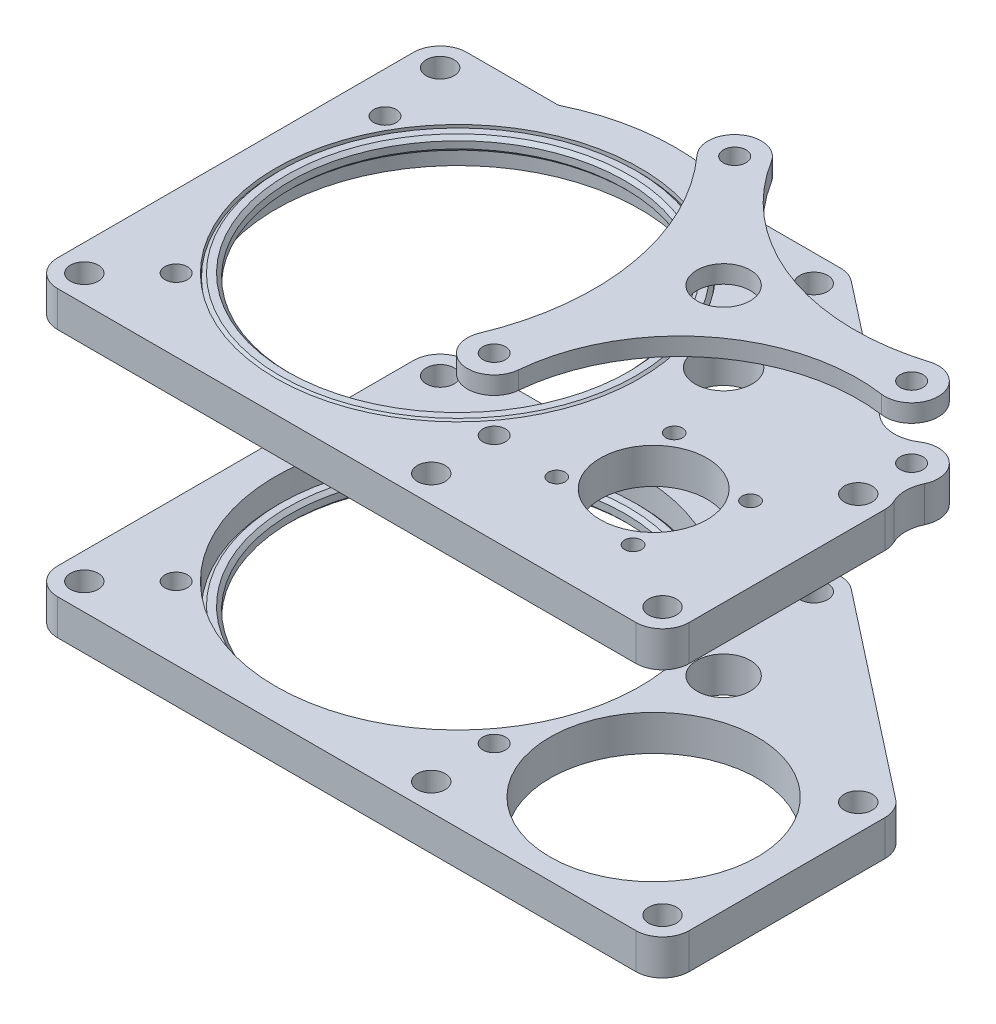
SolidWorks part; units mm, degrees
other "Stage 2 Retaining Plate"
other "Outer Top Plate"
other "Outer Bottom Plate"
other "Top Bearing Retainer"
other "Bottom Bearing Retainer"
material "Alum Plate"
ref_plane "Front Plane" through (0, 0, 0) normal (0, 0, 1) x (1, 0, 0)
ref_plane "Top Plane" through (0, 0, 0) normal (0, 1, 0) x (1, 0, 0)
ref_plane "Right Plane" through (0, 0, 0) normal (1, 0, 0) x (0, 0, -1)
other "Bounding Box"
ref_plane "Default Plane" through (-8.9266, -12.7485, 0) normal (-0.1736, 0.9848, 0) x (0.9848, 0.1736, 0)
sketch "Sketch1" plane through (0, 0, 0) normal (0, 1, 0) x (1, 0, 0)
  line L0 (-38.1, 76.2) -> (-38.1, -38.1)
  line L1 (-38.1, -38.1) -> (76.2, -38.1)
  line L2 (-38.1, 0) -> (0, 0) construction
  line L3 (0, 0) -> (0, -38.1) construction
  line L5 (-38.1, -38.1) -> (-33.3375, -33.3375) construction
  line L6 (-33.3375, -33.3375) -> (-33.3375, 0) construction
  line L7 (-33.3375, 0) -> (-33.3375, 30.1625) construction
  line L8 (-33.3375, -33.3375) -> (0, -33.3375) construction
  line L9 (0, -33.3375) -> (28.575, -33.3375) construction
  line L10 (28.575, -33.3375) -> (69.85, -33.3375) construction
  line L11 (-33.3375, 34.925) -> (-38.1, 34.925) construction
  circle A0 centre (0, 0) radius 32.5
  circle A1 centre (0, 0) radius 25
  circle A3 centre (50.8, -15.875) radius 17.5006
  circle A4 centre (0, 0) radius 31.115
  circle A5 centre (50.8, -15.875) radius 6.35
  circle A6 centre (38.3007, 9.1132) radius 8.255
  circle A7 centre (38.3007, 9.1132) radius 21.59
  circle A8 centre (-33.3375, -33.3375) radius 4.7625
  circle A9 centre (-33.3375, 30.1625) radius 4.7625
  circle A10 centre (69.85, -33.3375) radius 4.7625
  circle A12 centre (28.575, -33.3375) radius 4.7625
  point P24 (32.5, 0)
  point P26 (-32.5, 0)
  point P27 (33.2994, -15.875)
  point P38 (68.3006, -15.875)
  dimension "D1" = 65
  dimension "D2" = 50
  dimension "D3" = 35.0012
  dimension "D4" = 62.23
  dimension "D5" = 12.7
  dimension "D6" = 16.51
  dimension "D8" = 9.525
  dimension "D9" = 43.18
  dimension "D7" = 38.1
  dimension "D10" = 114.3
  dimension "D11" = 88.9
  dimension "D12" = 73.025
  dimension "D13" = 22.225
  dimension "D14" = 107.95
  dimension "D15" = 66.675
sketch "Sketch2" plane through (0, 0, 0) normal (0, 0, 1) x (1, 0, 0)
  line L0 (0, 0) -> (0, 19.05) construction
  line L1 (0, 19.05) -> (0, 24.1) construction
  line L2 (-32.5, 31.1) -> (32.5, 31.1)
  line L3 (-32.5, 31.1) -> (-32.5, 24.1)
  line L4 (-32.5, 24.1) -> (32.5, 24.1)
  line L5 (32.5, 31.1) -> (32.5, 24.1)
  line L6 (-32.5, 31.1) -> (32.5, 24.1) construction
  line L7 (-32.5, 24.1) -> (32.5, 31.1) construction
  line L8 (-32.5, 73.025) -> (32.5, 73.025)
  line L9 (-32.5, 73.025) -> (-32.5, 66.025)
  line L10 (-32.5, 66.025) -> (32.5, 66.025)
  line L11 (32.5, 73.025) -> (32.5, 66.025)
  line L12 (-32.5, 73.025) -> (32.5, 66.025) construction
  line L13 (-32.5, 66.025) -> (32.5, 73.025) construction
  line L14 (0, 31.1) -> (0, 66.025) construction
  line L15 (33.2994, 34.6047) -> (38.989, 24.75)
  line L16 (-38.1, 21.575) -> (101.6, 21.575)
  line L17 (-38.1, 21.575) -> (-38.1, 27.925)
  line L18 (-38.1, 27.925) -> (101.6, 27.925)
  line L19 (101.6, 21.575) -> (101.6, 27.925)
  line L20 (-38.1, 75.55) -> (101.6, 75.55)
  line L21 (-38.1, 75.55) -> (-38.1, 69.2)
  line L22 (-38.1, 69.2) -> (101.6, 69.2)
  line L23 (101.6, 75.55) -> (101.6, 69.2)
  line L24 (38.989, 24.75) -> (62.611, 24.75)
  line L25 (33.2994, 34.6047) -> (33.2994, 69.2)
  line L26 (33.2994, 69.2) -> (68.3006, 69.2)
  line L27 (68.3006, 34.6047) -> (68.3006, 69.2)
  line L28 (36.5821, 28.9189) -> (68.3006, 69.2) construction
  line L29 (33.2994, 69.2) -> (65.0179, 28.9189) construction
  line L30 (68.3006, 34.6047) -> (62.611, 24.75)
  line L31 (33.2994, 24.75) -> (33.2994, 34.6047) construction
  line L32 (33.2994, 24.75) -> (36.5821, 28.9189) construction
  line L33 (33.2994, 24.75) -> (38.989, 24.75) construction
  line L34 (62.611, 24.75) -> (68.3006, 24.75) construction
  line L35 (65.0179, 28.9189) -> (68.3006, 24.75) construction
  line L36 (68.3006, 24.75) -> (68.3006, 34.6047) construction
  line L37 (50.8, 24.75) -> (50.8, 69.2) construction
  line L38 (0, 0) -> (-69.131, 0) construction
  line L39 (-61.9887, 88.9) -> (127.3908, 88.9) construction
  line L40 (-32.5, 24.1) -> (-32.5, 21.575) construction
  line L41 (0, 88.25) -> (50.8, 88.25)
  line L42 (0, 88.25) -> (0, 85.075)
  line L43 (0, 85.075) -> (50.8, 85.075)
  line L44 (50.8, 88.25) -> (50.8, 85.075)
  line L45 (0, 88.25) -> (50.8, 85.075) construction
  line L46 (0, 85.075) -> (50.8, 88.25) construction
  line L47 (-32.5, 73.025) -> (-32.5, 75.55) construction
  circle A0 centre (0, 19.05) radius 19.05
  point P3 (0, 27.6)
  point P9 (0, 69.525)
  point P32 (50.8, 46.975)
  point P43 (25.4, 86.6625)
  dimension "D1" = 38.1
  dimension "D2" = 7
  dimension "D3" = 34.925
  dimension "D4" = 73.025
  dimension "D5" = 88.9
  dimension "D6" = 6.35
  dimension "D7" = 30
  dimension "D8" = 44.45
  dimension "D9" = 23.622
  dimension "D10" = 9.525
  dimension "D11" = 3.175
  dimension "D12" = 41.275
  dimension "D13" = 101.6
ref_plane "Plane1" through (0, 27.925, 0) normal (0, 1, 0) x (1, 0, 0)
sketch "Sketch3" plane through (0, 27.925, 0) normal (0, 1, 0) x (1, 0, 0)
  line L0 (-38.1, 76.2) -> (-38.1, -38.1) construction
  line L1 (-38.1, -38.1) -> (76.2, -38.1) construction
  line L2 (-38.1, 30.1625) -> (-38.1, -33.3375)
  line L3 (-33.3375, -38.1) -> (69.85, -38.1)
  line L5 (-33.3375, 30.1625) -> (33.3375, 30.1625) construction
  line L6 (69.85, -33.3375) -> (69.85, 1.5875) construction
  line L7 (0, 0) -> (0, 30.1625) construction
  line L8 (50.8, -15.875) -> (69.85, -15.875) construction
  line L9 (-33.3375, 34.925) -> (-17.0167, 34.925)
  line L10 (36.2727, 33.913) -> (72.7852, 5.338)
  line L11 (74.6125, 1.5875) -> (74.6125, -33.3375)
  line L12 (17.0167, 34.925) -> (33.3375, 34.925)
  circle A0 centre (0, 0) radius 32.5 construction
  circle A1 centre (0, 0) radius 32.5
  circle A3 centre (-33.3375, -33.3375) radius 4.7625 construction
  arc A5 (-38.1, -33.3375) -> (-33.3375, -38.1) centre (-33.3375, -33.3375) ccw
  circle A6 centre (-33.3375, 30.1625) radius 2.4892
  circle A8 centre (-33.3375, -33.3375) radius 2.4892
  circle A9 centre (28.575, -33.3375) radius 2.4892
  circle A10 centre (50.8, -15.875) radius 18.5166
  circle A11 centre (38.3007, 9.1132) radius 4.7625
  circle A12 centre (50.8, -15.875) radius 17.5006 construction
  circle A13 centre (69.85, -33.3375) radius 2.4892
  circle A14 centre (69.85, 1.5875) radius 2.4892
  circle A15 centre (33.3375, 30.1625) radius 2.4892
  arc A16 (33.3375, 34.925) -> (36.2727, 33.913) centre (33.3375, 30.1625) cw
  arc A17 (74.6125, 1.5875) -> (72.7852, 5.338) centre (69.85, 1.5875) ccw
  arc A18 (-38.1, 30.1625) -> (-33.3375, 34.925) centre (-33.3375, 30.1625) cw
  circle A19 centre (-33.3375, 30.1625) radius 4.7625 construction
  arc A20 (69.85, -38.1) -> (74.6125, -33.3375) centre (69.85, -33.3375) ccw
  circle A21 centre (69.85, -33.3375) radius 4.7625 construction
  arc A22 (-17.0167, 34.925) -> (17.0167, 34.925) centre (0, 0) cw
  dimension "D1" = 4.9784
  dimension "D2" = 1.016
  dimension "D3" = 9.525
  dimension "D4" = 6.35
extrude "Boss-Extrude1" add sketch "Sketch3" against normal up to vertex (6.35 mm away) up to point (-38.1, 21.575, 0)
ref_plane "Plane2" through (0, 69.2, 0) normal (0, 1, 0) x (1, 0, 0)
sketch "Sketch4" plane through (0, 69.2, 0) normal (0, 1, 0) x (1, 0, 0)
  line L0 (23.8081, 25.1161) -> (22.5294, 26.5282) construction
  line L1 (65.097, 10.8113) -> (59.8475, 10.4786) construction
  line L2 (65.0938, 11.3573) -> (36.2727, 33.913)
  line L3 (17.0167, 34.925) -> (33.3375, 34.925)
  line L8 (-33.3375, -38.1) -> (69.85, -38.1)
  line L9 (74.6125, -33.3375) -> (74.6125, 1.5875)
  line L10 (72.7852, 5.338) -> (36.2727, 33.913)
  line L11 (33.3375, 34.925) -> (17.0167, 34.925)
  line L12 (-17.0167, 34.925) -> (-33.3375, 34.925)
  line L13 (-38.1, 30.1625) -> (-38.1, -33.3375)
  line L15 (-33.3375, -38.1) -> (69.85, -38.1)
  line L16 (74.6125, -33.3375) -> (74.6125, 1.5875)
  line L17 (72.7852, 5.338) -> (71.2307, 6.5545)
  line L19 (-17.0167, 34.925) -> (-33.3375, 34.925)
  line L20 (-38.1, 30.1625) -> (-38.1, -33.3375)
  circle A0 centre (33.3375, 30.1625) radius 2.4892 construction
  circle A1 centre (69.85, 1.5875) radius 2.4892 construction
  circle A2 centre (69.85, -33.3375) radius 2.4892 construction
  circle A3 centre (28.575, -33.3375) radius 2.4892 construction
  circle A4 centre (-33.3375, -33.3375) radius 2.4892 construction
  circle A5 centre (28.2957, -21.831) radius 3.2385 construction
  circle A6 centre (-33.3375, 30.1625) radius 2.4892 construction
  circle A7 centre (19.3325, 30.0582) radius 3.2385 construction
  arc A8 (-38.1, -33.3375) -> (-33.3375, -38.1) centre (-33.3375, -33.3375) ccw
  arc A9 (69.85, -38.1) -> (74.6125, -33.3375) centre (69.85, -33.3375) ccw
  arc A10 (74.6125, 1.5875) -> (72.7852, 5.338) centre (69.85, 1.5875) ccw
  arc A11 (36.2727, 33.913) -> (33.3375, 34.925) centre (33.3375, 30.1625) ccw
  arc A12 (17.0167, 34.925) -> (-17.0167, 34.925) centre (0, 0) ccw
  arc A13 (-33.3375, 34.925) -> (-38.1, 30.1625) centre (-33.3375, 30.1625) ccw
  arc A15 (-38.1, -33.3375) -> (-33.3375, -38.1) centre (-33.3375, -33.3375) ccw
  arc A16 (69.85, -38.1) -> (74.6125, -33.3375) centre (69.85, -33.3375) ccw
  arc A17 (74.6125, 1.5875) -> (72.7852, 5.338) centre (69.85, 1.5875) ccw
  arc A18 (36.2727, 33.913) -> (33.3375, 34.925) centre (33.3375, 30.1625) ccw
  arc A19 (17.0167, 34.925) -> (-17.0167, 34.925) centre (0, 0) ccw
  arc A20 (-33.3375, 34.925) -> (-38.1, 30.1625) centre (-33.3375, 30.1625) ccw
  circle A21 centre (33.3375, 30.1625) radius 2.4892
  circle A22 centre (69.85, 1.5875) radius 2.4892
  circle A23 centre (69.85, -33.3375) radius 2.4892
  circle A24 centre (28.575, -33.3375) radius 2.4892
  circle A25 centre (-33.3375, -33.3375) radius 2.4892
  circle A27 centre (-33.3375, 30.1625) radius 2.4892
  circle A28 centre (38.3007, 9.1132) radius 5.08
  circle A30 centre (50.8, -15.875) radius 9.525
  circle A31 centre (0, 0) radius 32.5 construction
  circle A32 centre (0, 0) radius 32.5
  circle A33 centre (19.3325, 30.0582) radius 2.0193
  arc A34 (20.2854, 25.392) -> (14.6913, 28.9899) centre (19.3325, 30.0582) ccw construction
  circle A36 centre (69.85, 11.1125) radius 2.0193
  arc A37 (71.2307, 6.5545) -> (65.0938, 11.3573) centre (69.85, 11.1125) ccw
  circle A38 centre (28.2957, -21.831) radius 2.0193
  circle A39 centre (28.2957, -21.831) radius 4.7625 construction
  circle A40 centre (50.8, -15.875) radius 18.5166 construction
  circle A41 centre (38.3007, 9.1132) radius 21.59 construction
  circle A42 centre (69.85, 1.5875) radius 4.7625 construction
  arc A43 (65.097, 10.8113) -> (69.85, 6.35) centre (69.85, 11.1125) ccw construction
  arc A44 (65.0938, 11.3573) -> (65.097, 10.8113) centre (69.85, 11.1125) ccw construction
  arc A45 (22.5294, 26.5282) -> (20.2854, 25.392) centre (19.3325, 30.0582) ccw construction
  arc A46 (14.6913, 28.9899) -> (22.5294, 26.5282) centre (19.3325, 30.0582) ccw construction
  circle A48 centre (-33.3375, 30.1625) radius 4.7625 construction
  arc A49 (69.85, 6.35) -> (71.2307, 6.5545) centre (69.85, 11.1125) ccw construction
  dimension "D2" = 10.16
  dimension "D3" = 19.05
  dimension "D5" = 4.0386
  dimension "D6" = 1.524
  dimension "D4" = 1.905
  dimension "D1" = 0
extrude "Boss-Extrude2" add sketch "Sketch4" along normal up to vertex (6.35 mm away) separate body up to point (-38.1, 75.55, 0)
ref_plane "Plane3" through (0, 85.075, 0) normal (0, 1, 0) x (1, 0, 0)
sketch "Sketch6" plane through (0, 85.075, 0) normal (0, 1, 0) x (1, 0, 0)
  circle A0 centre (38.3007, 9.1132) radius 4.7625 construction
  circle A1 centre (28.2957, -21.831) radius 2.0193 construction
  circle A2 centre (69.85, 11.1125) radius 2.0193 construction
  circle A3 centre (19.3325, 30.0582) radius 2.0193 construction
  circle A4 centre (38.3007, 9.1132) radius 4.7625
  circle A5 centre (28.2957, -21.831) radius 2.0193
  circle A6 centre (69.85, 11.1125) radius 2.0193
  circle A7 centre (19.3325, 30.0582) radius 2.0193
  arc A8 (23.3818, 32.5651) -> (15.8013, 26.8626) centre (19.3325, 30.0582) ccw
  arc A9 (68.4478, 15.6639) -> (69.1741, 6.3982) centre (69.85, 11.1125) cw
  arc A10 (23.8971, -20.0051) -> (33.0399, -22.2483) centre (28.2957, -21.831) ccw
  arc A11 (23.3818, 32.5651) -> (68.4478, 15.6639) centre (56.8561, 53.2887) ccw
  arc A12 (33.0399, -22.2483) -> (69.1741, 6.3982) centre (64.6678, -25.0304) cw
  arc A13 (23.8971, -20.0051) -> (15.8013, 26.8626) centre (-17.1563, -2.9636) ccw
  circle A16 centre (28.575, -33.3375) radius 4.7625 construction
  arc A18 (71.2307, 6.5545) -> (65.0938, 11.3573) centre (69.85, 11.1125) ccw construction
  dimension "D1" = 39.37
  dimension "D2" = 31.75
  dimension "D3" = 44.45
extrude "Boss-Extrude3" add sketch "Sketch6" along normal up to vertex (3.175 mm away) separate body up to point (50.8, 88.25, 0)
sketch "Sketch13" plane through (0, 75.55, 0) normal (0, 1, 0) x (1, 0, 0)
  circle A0 centre (0, 0) radius 32.5 construction
  circle A1 centre (0, 0) radius 32.373
  circle A2 centre (0, 0) radius 29.833
  dimension "D1" = 2.54
  dimension "D2" = 0.127
extrude "Boss-Extrude7" add sketch "Sketch13" against normal up to vertex (2.525 mm away) separate body up to point (-32.5, 73.025, 0)
sketch "Sketch14" plane through (0, 21.575, 0) normal (0, -1, 0) x (1, 0, 0)
  circle A1 centre (0, 0) radius 29.833 construction
  circle A2 centre (0, 0) radius 32.373
  circle A3 centre (0, 0) radius 29.833
  circle A5 centre (0, 0) radius 32.373 construction
extrude "Boss-Extrude8" add sketch "Sketch14" against normal up to vertex (2.525 mm away) separate body up to point (-32.5, 24.1, 0)
sketch "Sketch8" plane through (0, 75.55, 0) normal (0, 1, 0) x (1, 0, 0)
  line L0 (40.3166, -22.683) -> (43.992, -5.3916) construction
  line L1 (40.3166, -22.683) -> (57.608, -26.3584) construction
  line L2 (43.992, -5.3916) -> (61.2834, -9.067) construction
  line L3 (57.608, -26.3584) -> (61.2834, -9.067) construction
  line L4 (40.3166, -22.683) -> (61.2834, -9.067) construction
  line L5 (43.992, -5.3916) -> (57.608, -26.3584) construction
  line L6 (50.8, -15.875) -> (52.6377, -7.2293) construction
  line L7 (50.8, -15.875) -> (50.8, -6.35) construction
  circle A0 centre (50.8, -15.875) radius 9.525 construction
  circle A1 centre (43.992, -5.3916) radius 1.5
  circle A2 centre (61.2834, -9.067) radius 1.5
  circle A3 centre (57.608, -26.3584) radius 1.5
  circle A4 centre (40.3166, -22.683) radius 1.5
  point P1 (50.8, -15.875)
  dimension "D2" = 3
  dimension "D1" = 25
  dimension "D3" = 12
extrude "Cut-Extrude1" cut sketch "Sketch8" against normal through all
sketch "Sketch9" plane through (0, 75.55, 0) normal (0, 1, 0) x (1, 0, 0)
  line L0 (-26.826, 15.488) -> (-28.1458, 16.25) construction
  line L1 (10.0431, 30.9093) -> (9.5721, 29.4599) construction
  line L2 (-21.9033, -21.9033) -> (-22.981, -22.981) construction
  line L3 (17.7671, -25.3741) -> (18.6412, -26.6224) construction
  line L4 (0, 0) -> (0, 32.5) construction
  line L6 (-25.1452, -25.1452) -> (-33.3375, -33.3375) construction
  line L7 (-38.1, -38.1) -> (-33.3375, -33.3375) construction
  circle A0 centre (-25.1452, -25.1452) radius 2.0193
  circle A1 centre (20.3968, -29.1296) radius 2.0193 construction
  circle A2 centre (-30.7965, 17.7803) radius 2.0193
  circle A3 centre (10.9889, 33.8202) radius 2.0193 construction
  circle A4 centre (-30.7965, 17.7803) radius 4.5847 construction
  circle A5 centre (10.9889, 33.8202) radius 4.5847 construction
  circle A6 centre (-25.1452, -25.1452) radius 4.5847 construction
  circle A7 centre (20.3968, -29.1296) radius 4.5847 construction
  circle A8 centre (0, 0) radius 32.5 construction
  circle A9 centre (19.3325, 30.0582) radius 2.0193 construction
  circle A10 centre (28.2957, -21.831) radius 2.0193 construction
  circle A11 centre (19.3325, 30.0582) radius 2.0193
  circle A12 centre (28.2957, -21.831) radius 2.0193
  dimension "D1" = 4.0386
  dimension "D2" = 9.1694
  dimension "D3" = 1.524
  dimension "D4" = 18
  dimension "D5" = 60
  dimension "D6" = 145
extrude "Cut-Extrude2" cut sketch "Sketch9" against normal through all and the other way through all
sketch "Sketch10" [suppressed] plane through (0, 75.55, 0) normal (0, 1, 0) x (1, 0, 0)
  arc A0 (8.5338, 37.9012) -> (12.4606, 38.3496) centre (10.9889, 33.8202) cw
  arc A1 (17.4463, 34.7124) -> (-19.9483, 33.3375) centre (0, 0) ccw construction
  arc A2 (12.4606, 38.3496) -> (18.9643, 35.5854) centre (0, 0) cw
  arc A3 (24.7384, 33.3375) -> (17.4463, 34.7124) centre (20.5392, 31.0908) ccw construction
  arc A4 (18.9643, 35.5854) -> (17.4463, 34.7124) centre (20.5392, 31.0908) ccw
  arc A5 (17.4463, 34.7124) -> (8.5338, 37.9012) centre (0, 0) ccw
extrude "Boss-Extrude4" [suppressed] add sketch "Sketch10" against normal up to surface (6.35 mm away)
sketch "Sketch11" [suppressed] plane through (0, 27.925, 0) normal (0, 1, 0) x (1, 0, 0)
  line L0 (33.3375, 33.3375) -> (19.9483, 33.3375) construction
  line L1 (22.6842, 33.3375) -> (19.9483, 33.3375)
  arc A0 (12.4606, 38.3496) -> (8.5338, 37.9012) centre (10.9889, 33.8202) ccw construction
  arc A1 (12.4606, 38.3496) -> (8.5338, 37.9012) centre (10.9889, 33.8202) ccw
  arc A2 (19.9483, 33.3375) -> (-19.9483, 33.3375) centre (0, 0) ccw construction
  arc A3 (19.9483, 33.3375) -> (8.5338, 37.9012) centre (0, 0) ccw
  arc A4 (12.4606, 38.3496) -> (22.6842, 33.3375) centre (0, 0) cw
extrude "Boss-Extrude5" [suppressed] add sketch "Sketch11" against normal up to surface (6.35 mm away)
fillet "Fillet1" radius 6.35 2 edges at (65.0938, 72.375, -11.3573) (71.2307, 72.375, -6.5545)
chamfer "Chamfer2" distance 0.635 angle 45 4 edges at (0, 24.1, -32.373) (0, 24.1, -29.833) (0, 21.575, -32.373) (0, 21.575, -29.833)
chamfer "Chamfer1" distance 0.635 angle 45 4 edges at (0, 73.025, 32.373) (0, 73.025, 29.833) (0, 75.55, 32.373) (0, 75.55, 29.833)
other "Save Bodies1"
